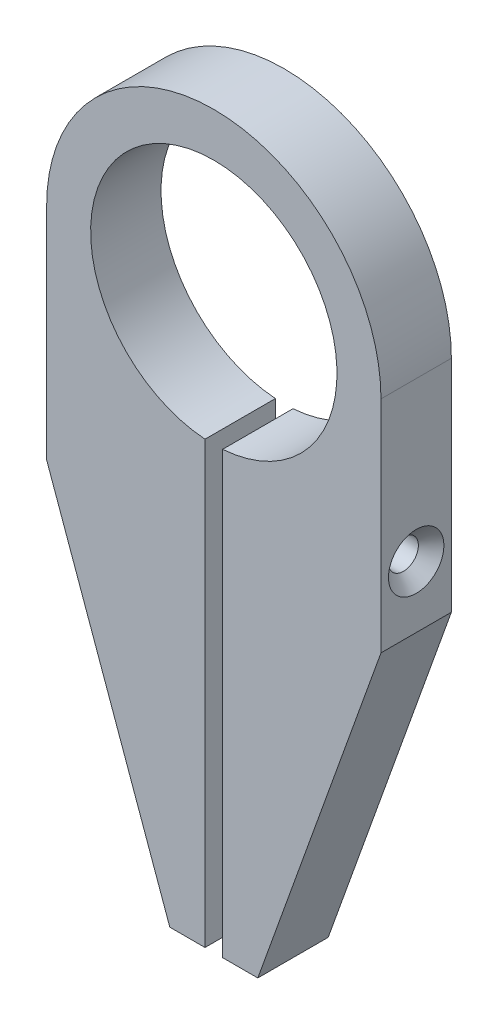
SolidWorks part; units mm, degrees
ref_plane "정면" through (0, 0, 0) normal (0, 0, 1) x (1, 0, 0)
ref_plane "윗면" through (0, 0, 0) normal (0, 1, 0) x (1, 0, 0)
ref_plane "우측면" through (0, 0, 0) normal (1, 0, 0) x (0, 0, -1)
sketch "스케치1" plane through (0, 0, 0) normal (0, 0, 1) x (1, 0, 0)
  line L3 (19, 0) -> (19, -25)
  line L4 (19, -25) -> (5, -64)
  line L5 (5, -64) -> (1, -64)
  line L6 (0, 0) -> (0, -73.734) construction
  line L7 (-1, 0) -> (1, 0)
  line L8 (-1, 0) -> (-1, -64)
  line L9 (-1, -64) -> (1, -64)
  line L10 (1, 0) -> (1, -64)
  line L11 (-5, -64) -> (-1, -64)
  line L12 (-19, -25) -> (-5, -64)
  line L13 (-19, 0) -> (-19, -25)
  circle A1 centre (0, 0) radius 14
  circle A2 centre (0, 0) radius 19
  point P6 (0, -64)
  point P12 (0, 0)
  dimension "D1" = 28
  dimension "D2" = 5
  dimension "D3" = 5
  dimension "D4" = 2
  dimension "D5" = 25
  dimension "D6" = 64
extrude "보스-돌출1" add sketch "스케치1" along normal blind 8
ref_plane "평면1" through (0, -14, 0) normal (0, 1, 0) x (1, 0, 0)
hole_wizard "M3 접시 머리 나사용 카운터싱크1" positions "스케치2" profile "스케치4" countersink size "M3" standard "ISO" end condition up to next
sketch "스케치2" plane through (19, 0, 0) normal (1, 0, 0) x (0, 0, -1)
  line L1 (-8, -25) -> (0, -25) construction
  line L2 (4.4, -14) -> (-4.4, -14) construction
  point P0 (-4, -18)
  point P8 (-4, -25)
  dimension "D1" = 4
sketch "스케치4" plane through (19, -18, 4) normal (0, 1, 0) x (0, 0, -1)
  line L0 (0, 0) -> (0, 18)
  line L1 (0, 18) -> (1.7, 18)
  line L2 (1.7, 18) -> (1.7, 1.45)
  line L3 (1.7, 1.45) -> (3.15, 0)
  line L5 (3.15, 0) -> (0, 0)
  line L6 (-1.7, 1.45) -> (-3.15, 0) construction
  line L11 (0, -6.35) -> (0, 107.95) construction
  dimension "관통 구멍 지름" = 3.4
  dimension "관통 구멍 깊이" = 18
  dimension "표면 카운터싱크 지름" = 6.3
  dimension "표면 카운터싱크 각도" = 90
hole_wizard "M3 나사 구멍1" positions "스케치5" profile "스케치7" tap size "M3" standard "ISO" end condition up to next
sketch "스케치5" plane through (-19, 0, 0) normal (-1, 0, 0) x (0, 0, 1)
  circle A2 centre (4, -18) radius 1.7 construction
  circle A3 centre (4, -18) radius 1.7
  point P0 (4, -18)
sketch "스케치7" plane through (-19, -18, 4) normal (0, 1, 0) x (0, 0, 1)
  line L0 (0, 0) -> (0, 18)
  line L1 (0, 18) -> (1.25, 18)
  line L2 (1.25, 18) -> (1.25, 0)
  line L5 (1.25, 0) -> (0, 0)
  line L11 (0, -6.35) -> (0, 107.95) construction
  dimension "관통 탭 드릴 지름" = 2.5
  dimension "관통 탭 드릴 깊이" = 18
cosmetic thread "구멍 나사산1" parameters "D2"=3
